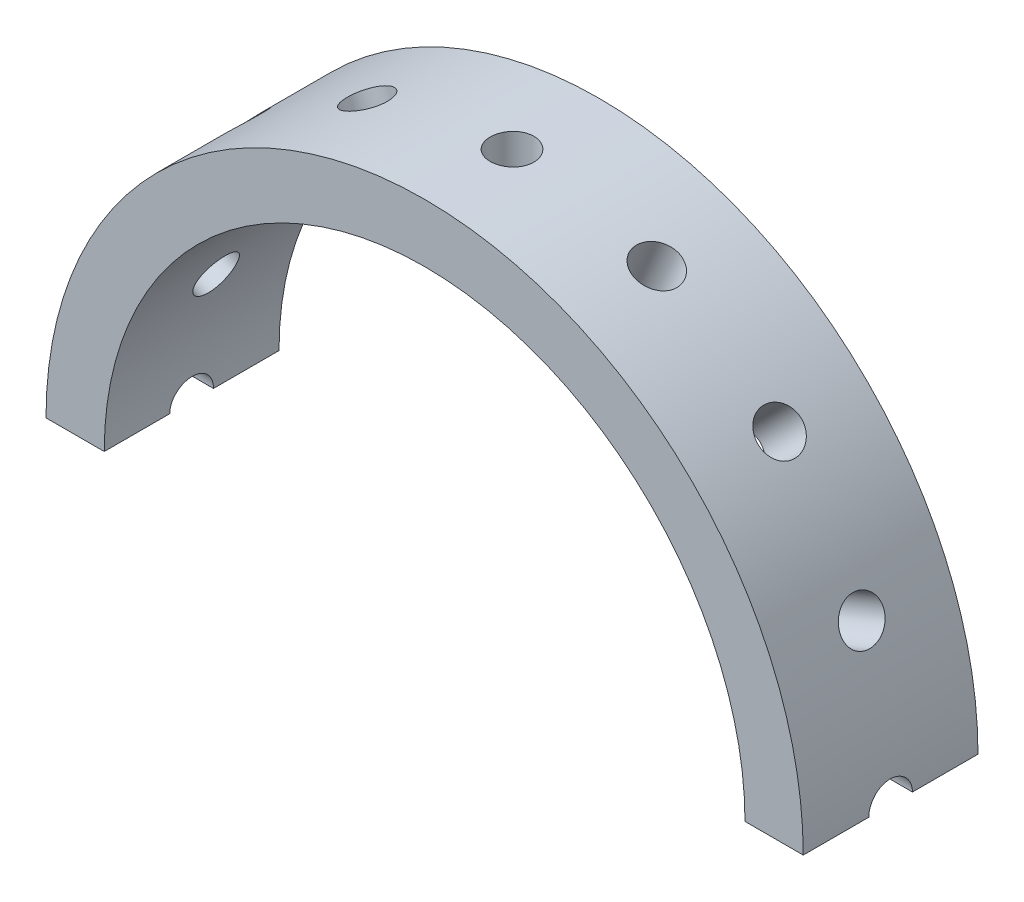
SolidWorks part; units mm, degrees
ref_plane "正面" through (0, 0, 0) normal (0, 0, 1) x (1, 0, 0)
ref_plane "平面" through (0, 0, 0) normal (0, 1, 0) x (1, 0, 0)
ref_plane "右側面" through (0, 0, 0) normal (1, 0, 0) x (0, 0, -1)
sketch "ｽｹｯﾁ1" plane through (0, 0, 0) normal (0, 0, 1) x (1, 0, 0)
  circle A0 centre (0, 0) radius 11
  circle A1 centre (0, 0) radius 13
  dimension "D1" = 22
  dimension "D2" = 26
extrude "ﾎﾞｽ - 押し出し1" add sketch "ｽｹｯﾁ1" along normal blind 6
sketch "ｽｹｯﾁ2" plane through (0, 0, 0) normal (0, 1, 0) x (1, 0, 0)
  line L0 (13, 0) -> (-13, 0) construction
  circle A0 centre (0, -3) radius 0.75
  dimension "D1" = 1.5
  dimension "D2" = 3
extrude "ｶｯﾄ - 押し出し1" cut sketch "ｽｹｯﾁ2" against normal through all
pattern_circular "円形ﾊﾟﾀｰﾝ1" count 16 over 360 about axis through (0, 0, 0) along (0, 0, 1) of "ｶｯﾄ - 押し出し1"
sketch "ｽｹｯﾁ3" plane through (0, 0, 0) normal (0, 1, 0) x (1, 0, 0)
  line L1 (18.3993, -8.0013) -> (-18.3993, -8.0013)
  line L2 (18.3993, -8.0013) -> (18.3993, 3.9448)
  line L3 (18.3993, 3.9448) -> (-18.3993, 3.9448)
  line L4 (-18.3993, -8.0013) -> (-18.3993, 3.9448)
  line L5 (18.3993, -8.0013) -> (-18.3993, 3.9448) construction
  line L6 (18.3993, 3.9448) -> (-18.3993, -8.0013) construction
  point P0 (0, -2.0282)
extrude "ｶｯﾄ - 押し出し2" cut sketch "ｽｹｯﾁ3" against normal through all
